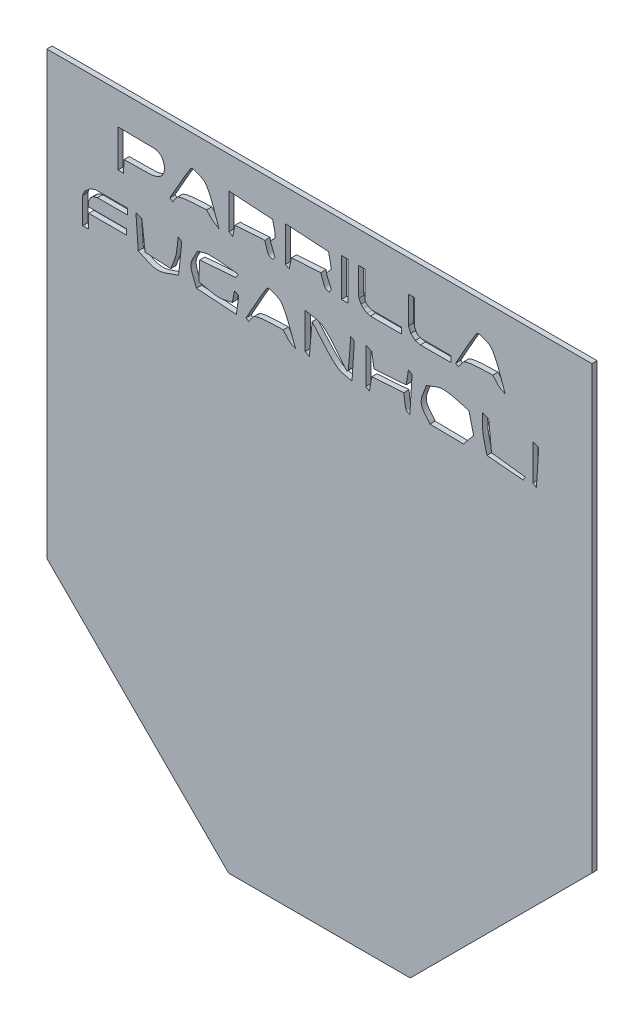
SolidWorks part; units mm, degrees
material "AISI 1020"
ref_plane "Front Plane" through (0, 0, 0) normal (0, 0, 1) x (1, 0, 0)
ref_plane "Top Plane" through (0, 0, 0) normal (0, 1, 0) x (1, 0, 0)
ref_plane "Right Plane" through (0, 0, 0) normal (1, 0, 0) x (0, 0, -1)
sketch "Sketch1" plane through (0, 0, 0) normal (0, 0, 1) x (1, 0, 0)
  line L0 (-167.5926, 115.2778) -> (42.4074, 115.2778)
  line L1 (-167.5926, 115.2778) -> (-167.5926, -184.7222)
  line L2 (-167.5926, -184.7222) -> (42.4074, -184.7222)
  line L3 (42.4074, -184.7222) -> (42.4074, 115.2778)
  dimension "D1" = 210
  dimension "D2" = 300
extrude "Boss-Extrude1" add sketch "Sketch1" against normal blind 2
sketch "Sketch3" plane through (0, 0, 0) normal (0, 0, 1) x (1, 0, 0)
  line L0 (-167.5926, 115.2778) -> (-167.5926, -114.7222)
  line L1 (-167.5926, 115.2778) -> (-167.5926, -184.7222) construction
  line L2 (-167.5926, -114.7222) -> (-97.5926, -114.7222)
  line L3 (-97.5926, -114.7222) -> (-27.5926, -114.7222)
  line L4 (-27.5926, -114.7222) -> (42.4074, -114.7222)
  line L5 (42.4074, -184.7222) -> (42.4074, 115.2778) construction
  line L6 (-97.5926, -114.7222) -> (-97.5926, -184.7222)
  line L12 (-167.5926, -184.7222) -> (42.4074, -184.7222) construction
  line L13 (-167.5926, -114.7222) -> (-97.5926, -184.7222)
  line L14 (-62.5926, -165.5644) -> (-62.1471, -165.5644)
  line L15 (-27.5926, -114.7222) -> (-27.5926, -184.7222)
  line L17 (-97.5926, -184.7222) -> (-27.5926, -184.7222)
  line L20 (-27.5926, -184.7222) -> (42.4074, -114.7222)
  dimension "D1" = 230
  dimension "D2" = 70
  dimension "D3" = 70
extrude "Cut-Extrude1" cut sketch "Sketch3" against normal blind 2
sketch "Sketch4" plane through (0, 0, -2) normal (0, 0, -1) x (-1, 0, 0)
  line L0 (97.5926, -184.7222) -> (97.5926, -174.7222)
  line L1 (27.5926, -184.7222) -> (27.5926, -174.7222)
  line L2 (-7.4074, -149.7222) -> (-2.4577, -144.7725)
  line L3 (27.5926, -184.7222) -> (-42.4074, -114.7222) construction
  line L4 (-42.4074, -114.7222) -> (-32.4074, -114.7222)
  line L5 (167.5926, -114.7222) -> (157.5926, -114.7222)
  line L6 (132.5926, -149.7222) -> (127.6428, -144.7725)
  line L7 (167.5926, -114.7222) -> (97.5926, -184.7222) construction
  line L8 (-32.4074, -114.7222) -> (-32.4074, -64.7222)
  line L9 (-32.4074, -64.7222) -> (-32.4074, -14.7222)
  line L10 (-32.4074, -14.7222) -> (-32.4074, 35.2778)
  line L11 (157.5926, -114.7222) -> (157.5926, -64.7222)
  line L12 (157.5926, -64.7222) -> (157.5926, -14.7222)
  line L13 (157.5926, -14.7222) -> (157.5926, 35.2778)
  circle A0 centre (97.5926, -174.7222) radius 5
  circle A1 centre (27.5926, -174.7222) radius 5
  circle A2 centre (-2.4577, -144.7725) radius 5
  circle A3 centre (127.6428, -144.7725) radius 5
  circle A4 centre (157.5926, -114.7222) radius 5
  circle A5 centre (157.5926, -64.7222) radius 5
  circle A6 centre (157.5926, -14.7222) radius 5
  circle A7 centre (157.5926, 35.2778) radius 5
  circle A8 centre (-32.4074, 35.2778) radius 5
  circle A9 centre (-32.4074, -14.7222) radius 5
  circle A10 centre (-32.4074, -64.7222) radius 5
  circle A11 centre (-32.4074, -114.7222) radius 5
  dimension "D13" = 10
  dimension "D14" = 10
  dimension "D15" = 10
  dimension "D16" = 10
  dimension "D17" = 10
  dimension "D18" = 10
  dimension "D19" = 10
  dimension "D20" = 10
  dimension "D21" = 10
  dimension "D22" = 10
  dimension "D23" = 10
  dimension "D24" = 10
  dimension "D1" = 10
  dimension "D2" = 7
  dimension "D3" = 10
  dimension "D4" = 10
  dimension "D5" = 7
  dimension "D6" = 10
  dimension "D7" = 50
  dimension "D8" = 50
  dimension "D9" = 50
  dimension "D10" = 50
  dimension "D11" = 50
  dimension "D12" = 50
extrude "Cut-Extrude2" cut sketch "Sketch4" against normal blind 0.1
sketch "Sketch5" plane through (0, 0, -2) normal (0, 0, -1) x (-1, 0, 0)
  line L0 (-42.4074, 115.2778) -> (-42.4074, 55.2778)
  line L1 (-42.4074, -114.7222) -> (-42.4074, 115.2778) construction
  line L2 (-42.4074, 55.2778) -> (167.5926, 55.2778)
  line L3 (167.5926, 115.2778) -> (167.5926, -114.7222) construction
  line L4 (167.5926, 55.2778) -> (167.5926, 115.2778)
  line L5 (167.5926, 115.2778) -> (-42.4074, 115.2778)
  dimension "D1" = 60
extrude "Cut-Extrude3" cut sketch "Sketch5" against normal blind 2
sketch "Sketch7" plane through (0, 0, 0) normal (0, 0, 1) x (1, 0, 0)
  line L0 (30.4175, 165.9978) -> (822.4175, 165.9978) construction
  line L1 (-137.8855, 33.2503) -> (-138.0623, 28.4776)
  line L2 (-138.0623, 28.4776) -> (-140.1835, 28.6544)
  line L3 (-140.1835, 28.6544) -> (-140.1835, 42.9725)
  line L4 (-119.1481, 28.4776) -> (-120.2087, 29.3614)
  line L7 (-97.4057, 42.9725) -> (-80.6128, 41.9119)
  line L8 (-81.4966, 34.3109) -> (-79.7289, 29.715)
  line L9 (-79.7289, 29.715) -> (-80.6128, 28.4776)
  line L10 (-83.6178, 33.4271) -> (-95.1077, 32.72)
  line L11 (-95.1077, 32.72) -> (-95.9916, 28.4776)
  line L12 (-95.9916, 28.4776) -> (-97.4057, 29.3614)
  line L13 (-97.4057, 29.3614) -> (-97.4057, 42.9725)
  line L14 (-75.6633, 42.9725) -> (-59.0471, 41.9119)
  line L15 (-59.0471, 41.9119) -> (-57.9865, 36.6089)
  line L16 (-57.9865, 36.6089) -> (-59.931, 34.3109)
  line L17 (-59.931, 34.3109) -> (-57.9865, 29.8917)
  line L18 (-57.9865, 29.8917) -> (-58.8704, 28.4776)
  line L19 (-62.0522, 33.4271) -> (-73.3653, 32.72)
  line L20 (-73.3653, 32.72) -> (-74.2492, 28.4776)
  line L21 (-74.2492, 28.4776) -> (-75.6633, 29.3614)
  line L22 (-75.6633, 29.3614) -> (-75.6633, 42.9725)
  line L23 (-54.0976, 43.1493) -> (-51.6229, 43.1493)
  line L24 (-51.6229, 43.1493) -> (-51.6229, 28.4776)
  line L25 (-51.6229, 28.4776) -> (-54.0976, 28.4776)
  line L26 (-54.0976, 28.4776) -> (-54.0976, 43.1493)
  line L27 (-47.3805, 43.1493) -> (-45.0825, 43.1493)
  line L28 (-45.0825, 43.1493) -> (-45.0825, 33.0735)
  line L29 (-42.2542, 30.7756) -> (-30.9411, 30.7756)
  line L30 (-30.9411, 30.7756) -> (-30.9411, 28.4776)
  line L31 (-30.9411, 28.4776) -> (-42.9613, 28.4776)
  line L32 (-47.3805, 32.1897) -> (-47.5572, 33.4271)
  line L33 (-47.5572, 33.4271) -> (-47.5572, 42.9725)
  line L34 (-28.2896, 43.1493) -> (-25.9916, 43.1493)
  line L35 (-25.9916, 43.1493) -> (-25.9916, 33.4271)
  line L36 (-23.1633, 30.7756) -> (-11.8502, 30.7756)
  line L37 (-11.8502, 30.7756) -> (-11.8502, 28.4776)
  line L38 (-11.8502, 28.4776) -> (-23.6936, 28.4776)
  line L39 (-28.2896, 32.5432) -> (-28.2896, 43.1493)
  line L40 (-9.0219, 28.4776) -> (-10.0825, 29.1847)
  line L43 (-148.8451, 17.6948) -> (-136.4714, 17.6948)
  line L44 (-136.4714, 17.6948) -> (-136.4714, 15.3968)
  line L45 (-136.4714, 15.3968) -> (-148.138, 15.3968)
  line L46 (-151.4966, 12.5685) -> (-151.4966, 10.6241)
  line L47 (-151.4966, 10.6241) -> (-137.0017, 10.6241)
  line L48 (-137.0017, 10.6241) -> (-137.0017, 8.5028)
  line L49 (-137.0017, 8.5028) -> (-151.4966, 8.5028)
  line L50 (-151.4966, 8.5028) -> (-151.4966, 3.1998)
  line L51 (-151.4966, 3.1998) -> (-153.7946, 3.1998)
  line L52 (-153.7946, 3.1998) -> (-153.7946, 13.2756)
  line L53 (-133.2896, 17.8715) -> (-130.9916, 16.9877)
  line L54 (-130.9916, 16.9877) -> (-129.7542, 6.3816)
  line L55 (-129.7542, 6.3816) -> (-119.8552, 5.8513)
  line L56 (-117.0269, 17.8715) -> (-115.6128, 16.9877)
  line L57 (-115.6128, 16.9877) -> (-116.8502, 5.1443)
  line L58 (-132.4057, 5.4978) -> (-133.2896, 17.8715)
  line L59 (-93.8704, 16.9877) -> (-94.7542, 15.3968)
  line L60 (-94.7542, 15.3968) -> (-108.7188, 14.3362)
  line L61 (-108.7188, 14.3362) -> (-109.0724, 6.9119)
  line L62 (-96.1683, 6.3816) -> (-95.2845, 10.8008)
  line L63 (-95.2845, 10.8008) -> (-93.6936, 9.917)
  line L64 (-93.6936, 9.917) -> (-94.5774, 3.1998)
  line L65 (-94.5774, 3.1998) -> (-109.9562, 4.2604)
  line L66 (-89.8047, 3.1998) -> (-90.8653, 3.9069)
  line L69 (-50.5623, 17.8715) -> (-49.1481, 16.9877)
  line L70 (-49.1481, 16.9877) -> (-50.032, 3.1998)
  line L71 (-65.4108, 15.3968) -> (-66.4714, 3.1998)
  line L72 (-66.4714, 3.1998) -> (-68.0623, 4.0836)
  line L73 (-68.0623, 4.0836) -> (-68.0623, 17.8715)
  line L74 (-44.7289, 17.8715) -> (-42.431, 16.9877)
  line L75 (-42.431, 16.9877) -> (-41.5471, 11.5079)
  line L76 (-41.5471, 11.5079) -> (-29.1734, 12.3917)
  line L77 (-29.1734, 12.3917) -> (-28.2896, 17.8715)
  line L78 (-28.2896, 17.8715) -> (-26.8754, 16.9877)
  line L79 (-26.8754, 16.9877) -> (-27.7593, 3.1998)
  line L80 (-30.0572, 9.3867) -> (-42.431, 8.5028)
  line L81 (-42.431, 8.5028) -> (-43.3148, 3.1998)
  line L82 (-43.3148, 3.1998) -> (-44.7289, 4.0836)
  line L83 (-44.7289, 4.0836) -> (-44.7289, 17.8715)
  line L84 (-4.9562, 15.9271) -> (-3.1885, 8.5028)
  line L85 (-3.1885, 8.5028) -> (-7.0774, 3.7301)
  line L86 (-7.0774, 3.7301) -> (-19.9815, 3.9069)
  line L89 (0.3468, 17.8715) -> (2.6448, 16.9877)
  line L90 (2.6448, 16.9877) -> (3.7054, 6.2049)
  line L91 (3.7054, 6.2049) -> (16.7862, 4.614)
  line L92 (16.7862, 4.614) -> (15.9024, 3.1998)
  line L93 (15.9024, 3.1998) -> (1.9377, 4.4372)
  line L94 (19.6145, 17.8715) -> (21.9125, 16.9877)
  line L95 (21.9125, 16.9877) -> (21.0286, 3.1998)
  line L96 (21.0286, 3.1998) -> (19.6145, 4.0836)
  line L97 (19.6145, 4.0836) -> (19.6145, 17.8715)
  line L98 (-42.9613, 28.4776) -> (-44.1953, 28.8235)
  line L99 (-44.1953, 28.8235) -> (-45.5851, 29.6266)
  line L100 (-45.5851, 29.6266) -> (-46.6044, 30.6395)
  line L101 (-46.6044, 30.6395) -> (-47.0121, 31.5846)
  line L102 (-47.0121, 31.5846) -> (-47.3805, 32.1897)
  line L103 (-42.2542, 30.7756) -> (-43.3148, 31.0728)
  line L104 (-43.3148, 31.0728) -> (-44.5103, 31.8872)
  line L105 (-44.5103, 31.8872) -> (-45.0825, 33.0735)
  line L106 (-23.1633, 30.7756) -> (-24.5214, 31.1562)
  line L107 (-24.5214, 31.1562) -> (-25.2569, 31.8872)
  line L108 (-25.2569, 31.8872) -> (-25.9916, 33.4271)
  line L109 (-23.6936, 28.4776) -> (-25.6242, 29.0187)
  line L110 (-25.6242, 29.0187) -> (-27.4086, 30.4619)
  line L111 (-27.4086, 30.4619) -> (-28.2896, 32.5432)
  line L112 (-151.4966, 12.5685) -> (-150.9054, 13.9035)
  line L113 (-150.9054, 13.9035) -> (-149.7338, 14.9135)
  line L114 (-149.7338, 14.9135) -> (-148.138, 15.3968)
  line L115 (-148.8451, 17.6948) -> (-150.9054, 16.9877)
  line L116 (-150.9054, 16.9877) -> (-151.9307, 16.1039)
  line L117 (-151.9307, 16.1039) -> (-153.0764, 15.1161)
  line L118 (-153.0764, 15.1161) -> (-153.6134, 13.9035)
  line L119 (-153.6134, 13.9035) -> (-153.7946, 13.2756)
  line L120 (-47.3805, 43.1493) -> (-47.5572, 42.9725)
  spline S0 degree 3 poles (-140.1835, 42.9725) (-135.2929, 42.9136) (-130.4013, 42.9122) (-125.5118, 42.7958) (-125.4285, 42.7938) (-125.4095, 42.6563) (-125.335, 42.619) (-124.3791, 42.141) (-123.8204, 42.1148) (-123.2138, 41.2049) (-121.852, 39.1621) (-121.8851, 35.8957) (-124.0976, 34.4877) (-125.0907, 33.8557) (-126.455, 33.4639) (-127.633, 33.4271) (-131.0493, 33.3203) (-134.468, 33.3092) (-137.8855, 33.2503) knots 0 0 0 0 1 1 1 2 2 2 3 3 3 4 4 4 5 5 5 6 6 6 6
  spline S1 degree 3 poles (-120.2087, 29.3614) (-117.5572, 33.8985) (-115.1435, 38.5831) (-112.2542, 42.9725) (-112.0184, 43.3308) (-111.4175, 43.4793) (-111.0168, 43.3261) (-109.3169, 42.6761) (-107.241, 42.1971) (-106.2441, 40.6746) (-103.8406, 37.0038) (-102.9444, 32.5432) (-101.2946, 28.4776) knots 0 0 0 0 1 1 1 2 2 2 3 3 3 4 4 4 4
  spline S2 degree 3 poles (-101.2946, 28.4776) (-102.0606, 28.949) (-102.8953, 29.3236) (-103.5926, 29.8917) (-104.497, 30.6286) (-105.2424, 31.5416) (-106.0673, 32.3665) knots 0 0 0 0 1 1 1 2 2 2 2
  spline S3 degree 3 poles (-106.0673, 32.3665) (-109.6027, 32.0129) (-113.2677, 32.3184) (-116.6734, 31.3059) (-117.8742, 30.9489) (-118.3232, 29.4203) (-119.1481, 28.4776) knots 0 0 0 0 1 1 1 2 2 2 2
  spline S5 degree 3 poles (-80.6128, 41.9119) (-80.3182, 40.0853) (-79.5152, 38.27) (-79.7289, 36.4321) (-79.8353, 35.5179) (-80.9074, 35.018) (-81.4966, 34.3109) knots 0 0 0 0 1 1 1 2 2 2 2
  spline S6 degree 3 poles (-80.6128, 28.4776) (-81.1431, 28.7722) (-81.8889, 28.8429) (-82.2037, 29.3614) (-82.9484, 30.5879) (-83.1465, 32.0719) (-83.6178, 33.4271) knots 0 0 0 0 1 1 1 2 2 2 2
  spline S7 degree 3 poles (-58.8704, 28.4776) (-59.4007, 28.7722) (-60.1332, 28.8511) (-60.4613, 29.3614) (-61.2482, 30.5856) (-61.5219, 32.0719) (-62.0522, 33.4271) knots 0 0 0 0 1 1 1 2 2 2 2
  spline S8 degree 3 poles (-10.0825, 29.1847) (-7.431, 33.7806) (-5.0584, 38.5492) (-2.1279, 42.9725) (-1.8596, 43.3776) (-1.172, 43.4878) (-0.7138, 43.3261) (0.927, 42.747) (2.929, 42.307) (3.8822, 40.8513) (6.3278, 37.1162) (7.2997, 32.6022) (9.0084, 28.4776) knots 0 0 0 0 1 1 1 2 2 2 3 3 3 4 4 4 4
  spline S9 degree 3 poles (9.0084, 28.4776) (8.2424, 28.89) (7.3849, 29.1654) (6.7104, 29.715) (5.7732, 30.4786) (5.0606, 31.4826) (4.2357, 32.3665) knots 0 0 0 0 1 1 1 2 2 2 2
  spline S10 degree 3 poles (4.2357, 32.3665) (0.7003, 32.0719) (-2.9662, 32.4812) (-6.3704, 31.4826) (-7.6522, 31.1066) (-8.138, 29.4793) (-9.0219, 28.4776) knots 0 0 0 0 1 1 1 2 2 2 2
  spline S12 degree 3 poles (-119.8552, 5.8513) (-119.2071, 7.619) (-118.342, 9.3216) (-117.9108, 11.1544) (-117.3935, 13.3527) (-117.3215, 15.6325) (-117.0269, 17.8715) knots 0 0 0 0 1 1 1 2 2 2 2
  spline S13 degree 3 poles (-116.8502, 5.1443) (-119.6195, 4.3783) (-122.2856, 2.781) (-125.1582, 2.8463) (-127.73, 2.9047) (-129.9899, 4.614) (-132.4057, 5.4978) knots 0 0 0 0 1 1 1 2 2 2 2
  spline S14 degree 3 poles (-109.6027, 16.8109) (-108.1296, 17.1645) (-106.6983, 17.8545) (-105.1835, 17.8715) (-101.4012, 17.914) (-97.6414, 17.2823) (-93.8704, 16.9877) knots 0 0 0 0 1 1 1 2 2 2 2
  spline S15 degree 3 poles (-109.0724, 6.9119) (-106.5387, 6.4406) (-104.0463, 5.6036) (-101.4714, 5.4978) (-99.6808, 5.4242) (-97.936, 6.087) (-96.1683, 6.3816) knots 0 0 0 0 1 1 1 2 2 2 2
  spline S16 degree 3 poles (-109.9562, 4.2604) (-110.6633, 6.4995) (-112.1435, 8.6305) (-112.0774, 10.9776) (-112.018, 13.0889) (-110.4276, 14.8665) (-109.6027, 16.8109) knots 0 0 0 0 1 1 1 2 2 2 2
  spline S17 degree 3 poles (-90.8653, 3.9069) (-88.2138, 8.5028) (-85.8025, 13.246) (-82.9108, 17.6948) (-82.677, 18.0544) (-82.0765, 18.1949) (-81.6734, 18.0483) (-80.0382, 17.4537) (-78.0426, 17.0213) (-77.0774, 15.5735) (-74.5883, 11.8398) (-73.5421, 7.3244) (-71.7744, 3.1998) knots 0 0 0 0 1 1 1 2 2 2 3 3 3 4 4 4 4
  spline S18 degree 3 poles (-71.7744, 3.1998) (-72.5404, 3.6123) (-73.3979, 3.8876) (-74.0724, 4.4372) (-75.0096, 5.2009) (-75.7222, 6.2049) (-76.5471, 7.0887) knots 0 0 0 0 1 1 1 2 2 2 2
  spline S19 degree 3 poles (-76.5471, 7.0887) (-80.0825, 6.7941) (-83.749, 7.2034) (-87.1532, 6.2049) (-88.435, 5.8289) (-88.9209, 4.2015) (-89.8047, 3.1998) knots 0 0 0 0 1 1 1 2 2 2 2
  spline S21 degree 3 poles (-68.0623, 17.8715) (-65.7643, 17.2234) (-63.0608, 17.3829) (-61.1683, 15.9271) (-57.4954, 13.1017) (-55.0404, 8.9742) (-51.9764, 5.4978) knots 0 0 0 0 1 1 1 2 2 2 2
  spline S22 degree 3 poles (-51.9764, 5.4978) (-51.7997, 5.7924) (-51.4851, 6.0403) (-51.4461, 6.3816) (-51.01, 10.1981) (-50.8569, 14.0416) (-50.5623, 17.8715) knots 0 0 0 0 1 1 1 2 2 2 2
  spline S23 degree 3 poles (-50.032, 3.1998) (-51.9764, 3.848) (-54.2594, 3.8706) (-55.8653, 5.1443) (-59.5238, 8.0458) (-62.2289, 11.9793) (-65.4108, 15.3968) knots 0 0 0 0 1 1 1 2 2 2 2
  spline S24 degree 3 poles (-27.7593, 3.1998) (-28.2306, 3.4944) (-28.9798, 3.5626) (-29.1734, 4.0836) (-29.7974, 5.7636) (-29.7626, 7.619) (-30.0572, 9.3867) knots 0 0 0 0 1 1 1 2 2 2 2
  spline S25 degree 3 poles (-21.3956, 16.1039) (-19.2155, 16.752) (-17.1295, 18.0728) (-14.8552, 18.0483) (-11.4808, 18.012) (-8.2559, 16.6342) (-4.9562, 15.9271) knots 0 0 0 0 1 1 1 2 2 2 2
  spline S26 degree 3 poles (-19.9815, 3.9069) (-21.101, 5.6746) (-23.0991, 7.1315) (-23.3401, 9.2099) (-23.615, 11.5817) (-22.0438, 13.8059) (-21.3956, 16.1039) knots 0 0 0 0 1 1 1 2 2 2 2
  spline S29 degree 3 poles (1.9377, 4.4372) (1.4074, 6.853) (0.6377, 9.2285) (0.3468, 11.6847) (0.1043, 13.7326) (0.3468, 15.8092) (0.3468, 17.8715) knots 0 0 0 0 1 1 1 2 2 2 2
extrude "Cut-Extrude4" cut sketch "Sketch7" against normal blind 2
